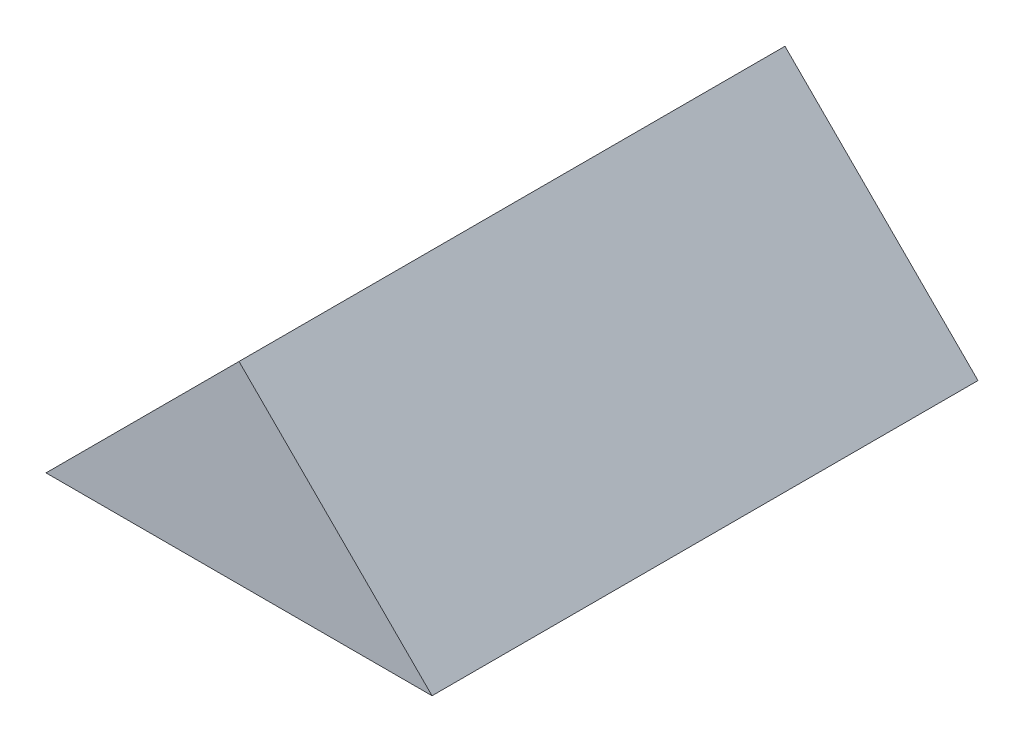
SolidWorks part; units mm, degrees
ref_plane "Front Plane" through (0, 0, 0) normal (0, 0, 1) x (1, 0, 0)
ref_plane "Top Plane" through (0, 0, 0) normal (0, 1, 0) x (1, 0, 0)
ref_plane "Right Plane" through (0, 0, 0) normal (1, 0, 0) x (0, 0, -1)
sketch "Sketch1" plane through (0, 0, 0) normal (0, 0, 1) x (1, 0, 0)
  line L0 (-17.9605, 0) -> (17.9605, 0)
  line L2 (0, 17.9605) -> (-17.9605, 0)
  line L3 (0, 17.9605) -> (0, 0) construction
  line L4 (0, 17.9605) -> (17.9605, 0)
  point P3 (0, 0)
  point P6 (0, 0)
  point P8 (-9.4779, 0)
  dimension "D1" = 25.4
  dimension "D2" = 45
extrude "Boss-Extrude1" add sketch "Sketch1" along normal mid plane 50.8
